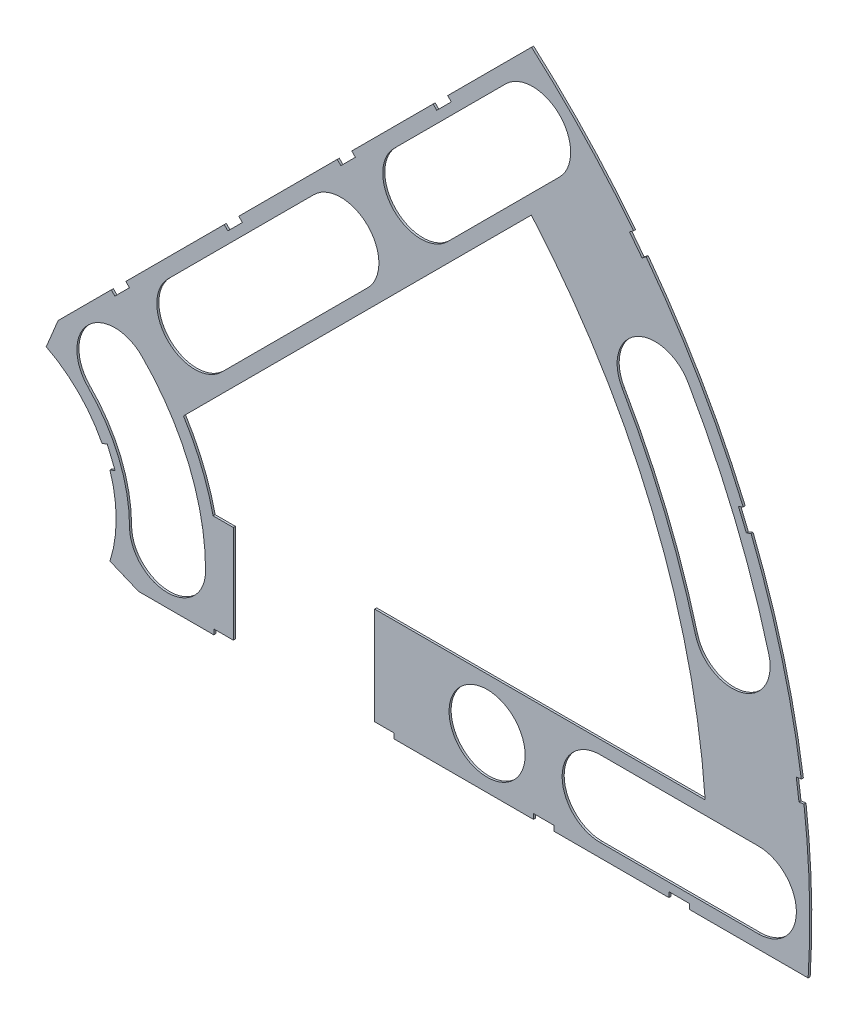
SolidWorks part; units mm, degrees
material "PTFE (general)"
ref_plane "Front Plane" through (0, 0, 0) normal (0, 0, 1) x (1, 0, 0)
ref_plane "Top Plane" through (0, 0, 0) normal (0, 1, 0) x (1, 0, 0)
ref_plane "Right Plane" through (0, 0, 0) normal (1, 0, 0) x (0, 0, -1)
sketch "Sketch1" plane through (0, 0, 0) normal (0, 0, 1) x (1, 0, 0)
  line L0 (0, 0) -> (320.3893, 0) construction
  line L1 (0, 0) -> (155.5285, 155.5285) construction
  line L2 (67.2115, 76.1917) -> (8.6967, 17.6769)
  line L3 (8.6967, 17.6769) -> (7.229, 14.1336)
  line L4 (101.4014, -6.35) -> (18.6489, -6.35)
  line L5 (15.1056, -4.8823) -> (18.6489, -6.35)
  line L6 (88.6729, 6.35) -> (27.8605, 6.35)
  line L9 (67.1914, 58.2111) -> (24.1905, 15.2102)
  line L10 (0, 0) -> (40.4486, 97.6516) construction
  line L11 (0, 0) -> (123.4567, -51.1374) construction
  line L18 (8.6967, 17.6769) -> (13.294, 8.6183) construction
  line L19 (18.6489, -6.35) -> (15.4943, 3.3063) construction
  line L20 (27.8605, 6.35) -> (27.7442, 6.7059) construction
  line L21 (24.1905, 15.2102) -> (24.3599, 14.8764) construction
  arc A0 (7.229, 14.1336) -> (15.1056, -4.8823) centre (0, 0) cw
  arc A1 (67.2115, 76.1917) -> (101.4014, -6.35) centre (0, 0) cw
  arc A2 (24.1905, 15.2102) -> (27.8605, 6.35) centre (0, 0) cw
  arc A3 (67.1914, 58.2111) -> (88.6729, 6.35) centre (0, 0) cw
  arc A8 (13.294, 8.6183) -> (15.4943, 3.3063) centre (0, 0) cw construction
  arc A9 (24.3599, 14.8764) -> (27.7442, 6.7059) centre (0, 0) cw construction
  dimension "D1" = 45
  dimension "D3" = 6.35
  dimension "D4" = 15.875
  dimension "D7" = 22.5
  dimension "D8" = 101.6
  dimension "D11" = 12.7
  dimension "D12" = 12.7
  dimension "D2" = 6.35
  dimension "D5" = 67.5
  dimension "D9" = 1.27
  dimension "D10" = 1.27
  dimension "D6" = 12.7
extrude "Boss-Extrude1" add sketch "Sketch1" along normal blind 0.254
sketch "Sketch2" plane through (0, 0, 0.254) normal (0, 0, 1) x (1, 0, 0)
  line L0 (0, 0) -> (101.6, 0) construction
  line L1 (0, 0) -> (71.842, 71.842) construction
  line L3 (0, 0) -> (22.225, 0) construction
  line L4 (0, 0) -> (15.7154, 15.7154) construction
  line L5 (0, 0) -> (95.25, 0) construction
  line L6 (0, 0) -> (92.0044, 24.6525) construction
  arc A0 (101.4014, -6.35) -> (67.2115, 76.1917) centre (0, 0) ccw construction
  circle A1 centre (22.225, 0) radius 4.699
  arc A2 (15.1056, -4.8823) -> (7.229, 14.1336) centre (0, 0) ccw construction
  circle A3 centre (36.195, 0) radius 4.699
  circle A4 centre (61.722, 0) radius 4.699
  circle A5 centre (75.692, 0) radius 4.699
  circle A6 centre (95.25, 0) radius 4.699
  circle A7 centre (15.7154, 15.7154) radius 4.699
  circle A8 centre (25.5937, 25.5937) radius 4.699
  circle A9 centre (43.644, 43.644) radius 4.699
  circle A10 centre (53.5223, 53.5223) radius 4.699
  circle A11 centre (92.0044, 24.6525) radius 4.699
  circle A12 centre (82.4889, 47.625) radius 4.699
  circle A13 centre (67.3519, 67.3519) radius 4.699
  dimension "D3" = 9.398
  dimension "D1" = 45
  dimension "D2" = 6.35
  dimension "D4" = 6.35
  dimension "D5" = 13.97
  dimension "D7" = 13.97
  dimension "D8" = 19.558
  dimension "D9" = 45
  dimension "D10" = 15
  dimension "D11" = 25.527
  dimension "D6" = 2
extrude "Cut-Extrude1" cut sketch "Sketch2" against normal through all
sketch "Sketch3" plane through (0, 0, 0.254) normal (0, 0, 1) x (1, 0, 0)
  line L0 (15.2664, 24.2467) -> (17.0625, 26.0427)
  line L1 (15.2664, 24.2467) -> (15.7154, 23.7977)
  line L2 (17.0625, 26.0427) -> (17.5115, 25.5937)
  line L3 (15.7154, 23.7977) -> (17.5115, 25.5937)
  line L4 (67.2115, 76.1917) -> (8.6967, 17.6769) construction
  line L5 (44.9911, 53.9713) -> (43.195, 52.1753)
  line L6 (44.9911, 53.9713) -> (45.4401, 53.5223)
  line L7 (43.195, 52.1753) -> (43.644, 51.7263)
  line L8 (45.4401, 53.5223) -> (43.644, 51.7263)
  line L9 (27.94, -6.35) -> (30.48, -6.35)
  line L10 (27.94, -6.35) -> (27.94, -5.715)
  line L11 (30.48, -6.35) -> (30.48, -5.715)
  line L12 (27.94, -5.715) -> (30.48, -5.715)
  line L13 (18.6489, -6.35) -> (101.4014, -6.35) construction
  line L14 (67.437, -6.35) -> (69.977, -6.35)
  line L15 (67.437, -6.35) -> (67.437, -5.715)
  line L16 (69.977, -6.35) -> (69.977, -5.715)
  line L17 (67.437, -5.715) -> (69.977, -5.715)
  line L18 (29.2307, 38.211) -> (31.0268, 40.007)
  line L19 (29.2307, 38.211) -> (29.6797, 37.762)
  line L20 (31.0268, 40.007) -> (31.4758, 39.558)
  line L21 (29.6797, 37.762) -> (31.4758, 39.558)
  line L22 (56.845, 65.8253) -> (55.049, 64.0292)
  line L23 (56.845, 65.8253) -> (57.294, 65.3763)
  line L24 (55.049, 64.0292) -> (55.498, 63.5802)
  line L25 (57.294, 65.3763) -> (55.498, 63.5802)
  line L26 (47.6885, -6.35) -> (50.2285, -6.35)
  line L27 (47.6885, -6.35) -> (47.6885, -5.715)
  line L28 (50.2285, -6.35) -> (50.2285, -5.715)
  line L29 (47.6885, -5.715) -> (50.2285, -5.715)
  line L30 (84.201, -6.35) -> (86.741, -6.35)
  line L31 (84.201, -6.35) -> (84.201, -5.715)
  line L32 (86.741, -6.35) -> (86.741, -5.715)
  line L33 (84.201, -5.715) -> (86.741, -5.715)
  line L34 (0, 0) -> (100.7308, 13.2615) construction
  line L35 (0, 0) -> (93.8662, 38.8806) construction
  line L36 (0, 0) -> (80.6047, 61.8502) construction
  line L37 (0, 0) -> (101.6, 0) construction
  line L38 (99.9355, 14.4377) -> (100.267, 11.9194)
  line L39 (99.9355, 14.4377) -> (101.1946, 14.6035)
  line L40 (100.267, 11.9194) -> (101.5261, 12.0852)
  line L41 (101.1946, 14.6035) -> (101.5261, 12.0852)
  line L42 (99.9355, 14.4377) -> (101.5261, 12.0852) construction
  line L43 (100.267, 11.9194) -> (101.1946, 14.6035) construction
  line L44 (93.7655, 37.4643) -> (94.9388, 37.9503)
  line L45 (93.7655, 37.4643) -> (92.7935, 39.811)
  line L46 (94.9388, 37.9503) -> (93.9668, 40.297)
  line L47 (92.7935, 39.811) -> (93.9668, 40.297)
  line L48 (93.7655, 37.4643) -> (93.9668, 40.297) construction
  line L49 (94.9388, 37.9503) -> (92.7935, 39.811) construction
  line L50 (79.3278, 62.4712) -> (80.874, 60.456)
  line L51 (79.3278, 62.4712) -> (80.3354, 63.2443)
  line L52 (80.874, 60.456) -> (81.8816, 61.2292)
  line L53 (80.3354, 63.2443) -> (81.8816, 61.2292)
  line L54 (79.3278, 62.4712) -> (81.8816, 61.2292) construction
  line L55 (80.874, 60.456) -> (80.3354, 63.2443) construction
  line L56 (13.5939, 7.0054) -> (14.5659, 4.6588)
  line L57 (13.5939, 7.0054) -> (14.7672, 7.4914)
  line L58 (14.5659, 4.6588) -> (15.7393, 5.1448)
  line L59 (14.7672, 7.4914) -> (15.7393, 5.1448)
  line L60 (13.5939, 7.0054) -> (15.7393, 5.1448) construction
  line L61 (14.5659, 4.6588) -> (14.7672, 7.4914) construction
  circle A0 centre (15.7154, 15.7154) radius 4.699 construction
  circle A1 centre (43.644, 43.644) radius 4.699 construction
  circle A2 centre (22.225, 0) radius 4.699 construction
  circle A3 centre (61.722, 0) radius 4.699 construction
  arc A4 (101.4014, -6.35) -> (67.2115, 76.1917) centre (0, 0) ccw construction
  arc A9 (15.1056, -4.8823) -> (7.229, 14.1336) centre (0, 0) ccw construction
  circle A10 centre (36.195, 0) radius 4.699 construction
  circle A11 centre (75.692, 0) radius 4.699 construction
  circle A12 centre (25.5937, 25.5937) radius 4.699 construction
  circle A13 centre (53.5223, 53.5223) radius 4.699 construction
  point P75 (14.6666, 6.0751)
  dimension "D2" = 5.715
  dimension "D3" = 2.54
  dimension "D6" = 5.715
  dimension "D8" = 0.635
  dimension "D9" = 5.715
  dimension "D12" = 5.715
  dimension "D4" = 7.5
  dimension "D5" = 22.5
  dimension "D7" = 37.5
  dimension "D10" = 90
  dimension "D11" = 1.27
  dimension "D14" = 0.635
  dimension "D15" = 90
  dimension "D18" = 0.635
  dimension "D19" = 90
  dimension "D22" = 0.635
  dimension "D20" = 1.27
  dimension "D17" = 0.635
  dimension "D13" = 11.4935
  dimension "D16" = 8.509
  dimension "D21" = 11.4935
  dimension "D23" = 8.509
extrude "Cut-Extrude2" cut sketch "Sketch3" against normal through all
sketch "Sketch5" plane through (0, 0, 0.254) normal (0, 0, 1) x (1, 0, 0)
  line L0 (27.8605, 6.35) -> (88.6729, 6.35) construction
  line L1 (30.353, -7.62) -> (47.8155, -7.62)
  line L2 (30.353, -7.62) -> (30.353, 7.62)
  line L3 (27.94, -5.715) -> (27.94, -6.35) construction
  line L4 (30.353, 7.62) -> (47.8155, 7.62)
  line L5 (47.8155, -7.62) -> (47.8155, 7.62)
  line L8 (30.48, -6.35) -> (47.6885, -6.35) construction
  line L10 (50.2285, -6.35) -> (50.2285, -5.715) construction
  dimension "D1" = 1.27
  dimension "D2" = 1.27
  dimension "D3" = 2.413
  dimension "D4" = 2.413
sketch "Sketch6" plane through (0, 0, 0.254) normal (0, 0, 1) x (1, 0, 0)
  line L0 (0, 0) -> (101.6, 0) construction
  line L1 (0, 0) -> (71.842, 71.842) construction
  line L2 (0, 0) -> (87.9882, 50.8) construction
  line L3 (0, 0) -> (98.1381, 26.296) construction
  line L4 (25.5937, 25.5937) -> (43.644, 43.644) construction
  line L5 (22.271, 28.9164) -> (40.3213, 46.9667)
  line L6 (28.9164, 22.271) -> (46.9667, 40.3213)
  line L7 (53.5223, 53.5223) -> (67.3519, 67.3519) construction
  line L8 (50.1996, 56.845) -> (64.0292, 70.6746)
  line L9 (56.845, 50.1996) -> (70.6746, 64.0292)
  line L13 (95.25, 0) -> (75.692, 0) construction
  line L14 (95.25, -4.699) -> (75.692, -4.699)
  line L15 (95.25, 4.699) -> (75.692, 4.699)
  arc A0 (79.8253, 62.8529) -> (67.2115, 76.1917) centre (0, 0) ccw construction
  arc A1 (15.7154, 15.7154) -> (22.225, 0) centre (0, 0) cw construction
  arc A2 (26.924, 0) -> (19.0381, 19.0381) centre (0, 0) ccw
  arc A3 (17.526, 0) -> (12.3928, 12.3928) centre (0, 0) ccw
  arc A4 (17.526, 0) -> (26.924, 0) centre (22.225, 0) ccw
  arc A5 (101.4014, -6.35) -> (100.8887, 12.0013) centre (0, 0) ccw construction
  arc A6 (19.0381, 19.0381) -> (12.3928, 12.3928) centre (15.7154, 15.7154) ccw
  arc A7 (93.3728, 40.0509) -> (81.3715, 60.8378) centre (0, 0) ccw construction
  arc A8 (100.5572, 14.5196) -> (94.3448, 37.7043) centre (0, 0) ccw construction
  arc A9 (82.4889, 47.625) -> (92.0044, 24.6525) centre (0, 0) cw construction
  arc A10 (96.5433, 25.8687) -> (86.5584, 49.9745) centre (0, 0) ccw
  arc A11 (87.4655, 23.4363) -> (78.4195, 45.2755) centre (0, 0) ccw
  arc A12 (87.4655, 23.4363) -> (96.5433, 25.8687) centre (92.0044, 24.6525) ccw
  arc A13 (86.5584, 49.9745) -> (78.4195, 45.2755) centre (82.4889, 47.625) ccw
  arc A14 (22.271, 28.9164) -> (28.9164, 22.271) centre (25.5937, 25.5937) ccw
  arc A15 (46.9667, 40.3213) -> (40.3213, 46.9667) centre (43.644, 43.644) ccw
  arc A16 (50.1996, 56.845) -> (56.845, 50.1996) centre (53.5223, 53.5223) ccw
  arc A17 (70.6746, 64.0292) -> (64.0292, 70.6746) centre (67.3519, 67.3519) ccw
  circle A18 centre (67.3519, 67.3519) radius 4.699 construction
  circle A19 centre (43.644, 43.644) radius 4.699 construction
  arc A20 (95.25, -4.699) -> (95.25, 4.699) centre (95.25, 0) ccw
  arc A21 (75.692, 4.699) -> (75.692, -4.699) centre (75.692, 0) ccw
  point P8 (20.5332, 8.5051)
  point P12 (87.9995, 36.4506)
  point P43 (34.6189, 34.6189)
  point P48 (60.4371, 60.4371)
  point P70 (85.471, 0)
  dimension "D2" = 9.398
  dimension "D5" = 9.398
  dimension "D1" = 45
  dimension "D3" = 9.398
  dimension "D4" = 9.398
extrude "Cut-Extrude4" cut sketch "Sketch6" against normal through all
extrude "Cut-Extrude5" cut sketch "Sketch5" against normal through all
equation "\"cSep\"= 1.005"
equation "\"D11@Sketch2\"=\"cSep\""
equation "\"cSep2\"= \"D8@Sketch2\""
equation "\"D13@Sketch3\"=\"cSep\"/2-.05"
equation "\"D16@Sketch3\"=\"cSep2\"/2-.05"
equation "\"D21@Sketch3\"=\"cSep\"/2-.05"
equation "\"D23@Sketch3\"=\"cSep2\"/2-.05"
